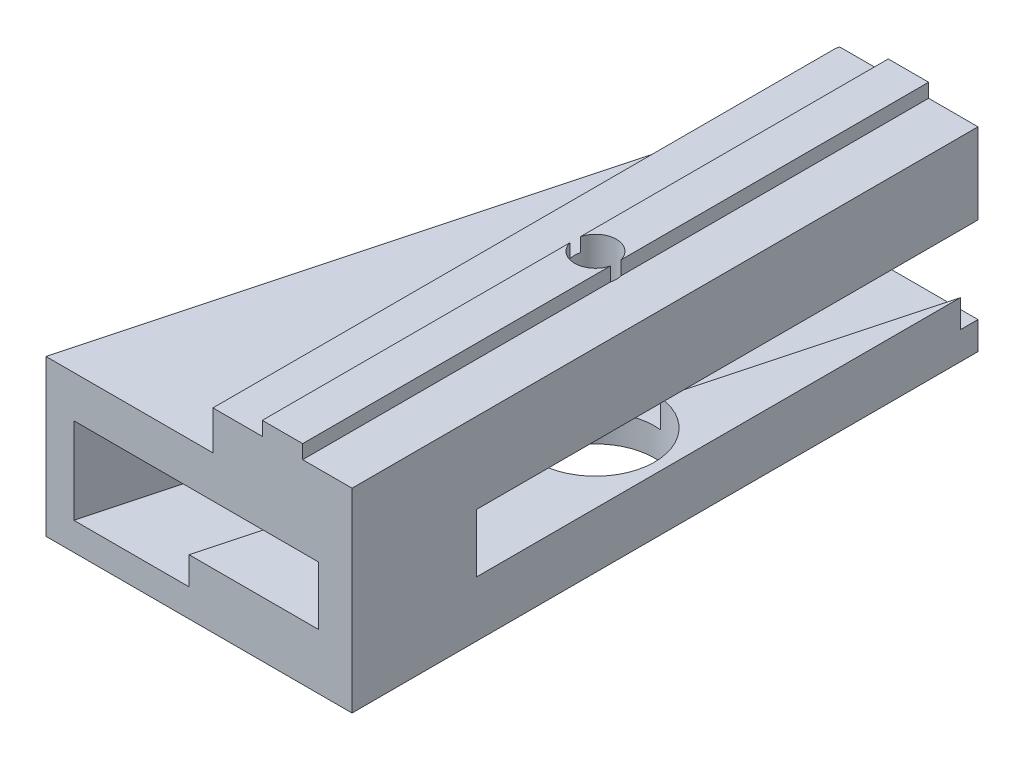
SolidWorks part; units mm, degrees
ref_plane "Front Plane" through (0, 0, 0) normal (0, 0, 1) x (1, 0, 0)
ref_plane "Top Plane" through (0, 0, 0) normal (0, 1, 0) x (1, 0, 0)
ref_plane "Right Plane" through (0, 0, 0) normal (1, 0, 0) x (0, 0, -1)
sketch "Sketch1" plane through (0, 0, 0) normal (0, 0, 1) x (1, 0, 0)
  line L0 (-11, 0) -> (11, 0)
  line L1 (11, 0) -> (11, 14)
  line L2 (11, 14) -> (7.45, 14)
  line L3 (7.45, 14) -> (7.45, 15)
  line L4 (7.45, 15) -> (4.55, 15)
  line L5 (4.55, 15) -> (4.55, 14)
  line L6 (4.55, 14) -> (-11, 14)
  line L7 (-11, 14) -> (-11, 0)
  point P9 (0, 0)
  dimension "D1" = 22
  dimension "D2" = 2.9
  dimension "D3" = 14
  dimension "D4" = 1
  dimension "D5" = 3.55
extrude "MakerBeamFix" add sketch "Sketch1" along normal mid plane 45
sketch "Sketch4" plane through (0, 0, 0) normal (0, -1, 0) x (1, 0, 0)
  line L1 (-11, 22.5) -> (-11, -22.5) construction
  line L2 (11, 22.5) -> (11, -22.5) construction
  circle A0 centre (6, 0) radius 1.5
  point P5 (-11, 0)
  dimension "D1" = 3
  dimension "D2" = 5
extrude "FixingHole" cut sketch "Sketch4" against normal through all
ref_plane "Plane1" through (0, 11, 0) normal (0, 1, 0) x (1, 0, 0)
sketch "Sketch5" plane through (0, 11, 0) normal (0, 1, 0) x (1, 0, 0)
  circle A0 centre (6, 0) radius 4.25
  circle A1 centre (6, 0) radius 1.5 construction
  dimension "D1" = 8.5
extrude "DriverHole" cut sketch "Sketch5" against normal through all
ref_plane "Plane2" through (0, 4, 0) normal (0, 1, 0) x (1, 0, 0)
sketch "Sketch6" plane through (0, 4, 0) normal (0, 1, 0) x (1, 0, 0)
  line L0 (7.4207, -26.8999) -> (-9, -22.5)
  line L1 (-9, -22.5) -> (3.5897, 24.4856)
  line L2 (3.5897, 24.4856) -> (20.0105, 20.0856)
  line L3 (20.0105, 20.0856) -> (7.4207, -26.8999)
  line L4 (-11, -22.5) -> (-11, 22.5) construction
  line L5 (-11, -22.5) -> (11, -22.5) construction
  dimension "D1" = 17
  dimension "D2" = 15
  dimension "D3" = 2
extrude "HoleForCalibers" cut sketch "Sketch6" along normal blind 4.2
sketch "Sketch7" plane through (0, 0, 0) normal (0, -1, 0) x (-1, 0, 0)
  line L0 (11, 22.5) -> (-1.0577, 22.5)
  line L1 (-1.0577, 22.5) -> (11, -22.5)
  line L2 (11, -22.5) -> (11, 22.5) construction
  line L3 (11, -22.5) -> (11, 22.5)
  line L5 (-3.0577, 22.5) -> (9, -22.5) construction
  line L6 (11, 22.5) -> (-11, 22.5) construction
extrude "Cut-Extrude2" cut sketch "Sketch7" against normal through all
sketch "Sketch8" plane through (0, 0, 22.5) normal (0, 0, 1) x (1, 0, 0)
  line L0 (11, 0) -> (11, 14) construction
  line L1 (-11, 14) -> (1, 14)
  line L2 (-11, 14) -> (-11, 11.2)
  line L3 (-11, 11.2) -> (1, 11.2)
  line L4 (1, 14) -> (1, 11.2)
  line L5 (-9, 8.2) -> (8.5997, 8.2) construction
  dimension "D1" = 10
  dimension "D2" = 3
extrude "Cut-Extrude3" cut sketch "Sketch8" against normal through all
ref_plane "Plane3" through (-6.2279, 0, 23.2428) normal (-0.2588, 0, 0.9659) x (0, -1, 0)
sketch "Sketch9" plane through (-6.2279, 0, 23.2428) normal (-0.2588, 0, 0.9659) x (0, -1, 0)
  line L1 (-2, -2.8699) -> (-4, -2.8699)
  line L2 (-2, -2.8699) -> (-2, 5.1301)
  line L3 (-2, 5.1301) -> (-4, 5.1301)
  line L4 (-4, -2.8699) -> (-4, 5.1301)
  point P5 (-4, -2.8699)
  dimension "D1" = 8
  dimension "D2" = 2
extrude "HoleForScrewOfCaliber" cut sketch "Sketch9" against normal through all
